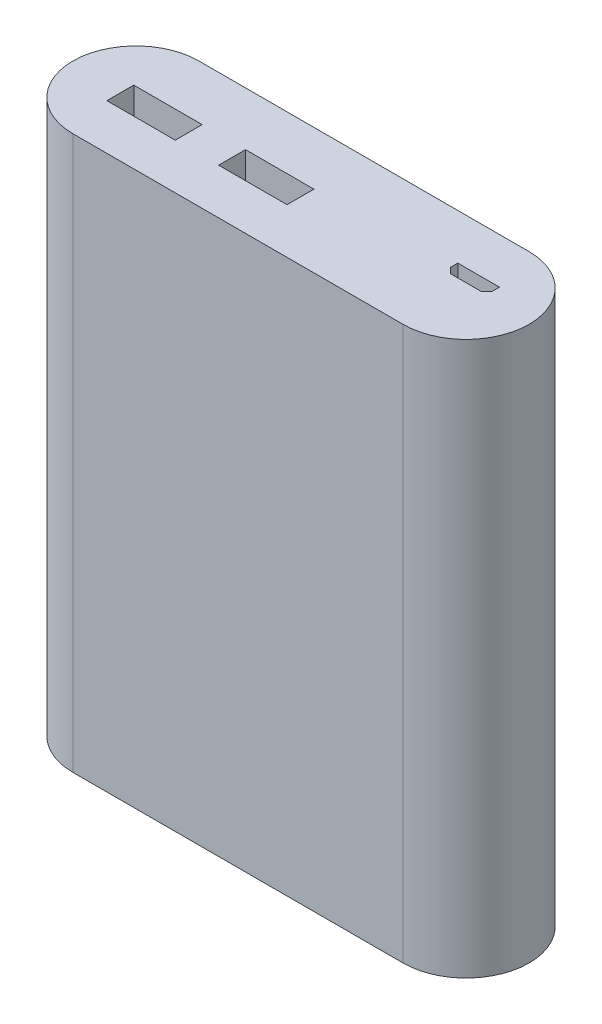
SolidWorks part; units mm, degrees
ref_plane "Front Plane" through (0, 0, 0) normal (0, 0, 1) x (1, 0, 0)
ref_plane "Top Plane" through (0, 0, 0) normal (0, 1, 0) x (1, 0, 0)
ref_plane "Right Plane" through (0, 0, 0) normal (1, 0, 0) x (0, 0, -1)
sketch "Sketch1" plane through (0, 0, 0) normal (0, 1, 0) x (1, 0, 0)
  line L0 (-28.95, 0) -> (28.95, 0) construction
  line L1 (-28.95, 11.05) -> (28.95, 11.05)
  line L2 (-28.95, -11.05) -> (28.95, -11.05)
  arc A0 (-28.95, 11.05) -> (-28.95, -11.05) centre (-28.95, 0) ccw
  arc A1 (28.95, -11.05) -> (28.95, 11.05) centre (28.95, 0) ccw
  point P2 (0, 0)
  dimension "D2" = 80
  dimension "D1" = 22.1
extrude "Boss-Extrude1" add sketch "Sketch1" along normal blind 97
sketch "Sketch2" plane through (0, 97, 0) normal (0, 1, 0) x (1, 0, 0)
  line L0 (-28.95, -11.05) -> (28.95, -11.05) construction
  line L1 (-31, 1.67) -> (-19, 1.67)
  line L2 (-31, 1.67) -> (-31, -3.05)
  line L3 (-31, -3.05) -> (-19, -3.05)
  line L4 (-19, 1.67) -> (-19, -3.05)
  line L5 (-31, 1.67) -> (-19, -3.05) construction
  line L6 (-31, -3.05) -> (-19, 1.67) construction
  line L7 (0.6, 1.67) -> (0.6, -3.05)
  line L8 (-11.4, 1.67) -> (0.6, 1.67)
  line L9 (-11.4, 1.67) -> (-11.4, -3.05)
  line L10 (-11.4, -3.05) -> (0.6, -3.05)
  line L11 (25.45, 0.8) -> (24.45, 1.8)
  line L12 (24.45, 1.8) -> (24.45, 3.05)
  line L13 (24.45, 3.05) -> (31.75, 3.05)
  line L14 (31.75, 3.05) -> (31.75, 1.8)
  line L15 (31.75, 1.8) -> (30.75, 0.8)
  line L16 (30.75, 0.8) -> (25.45, 0.8)
  line L17 (28.95, 11.05) -> (-28.95, 11.05) construction
  arc A1 (-28.95, 11.05) -> (-28.95, -11.05) centre (-28.95, 0) ccw construction
  arc A2 (28.95, -11.05) -> (28.95, 11.05) centre (28.95, 0) ccw construction
  point P0 (-25, -0.69)
  point P18 (28.1, 3.05)
  point P21 (28.1, 0.8)
  dimension "D1" = 8
  dimension "D2" = 9
  dimension "D3" = 4.72
  dimension "D4" = 12
  dimension "D6" = 7.6
  dimension "D7" = 8
  dimension "D8" = 8.25
  dimension "D9" = 2.25
  dimension "D10" = 7.3
  dimension "D11" = 1.25
  dimension "D5" = 2
extrude "Cut-Extrude1" cut sketch "Sketch2" against normal blind 10
